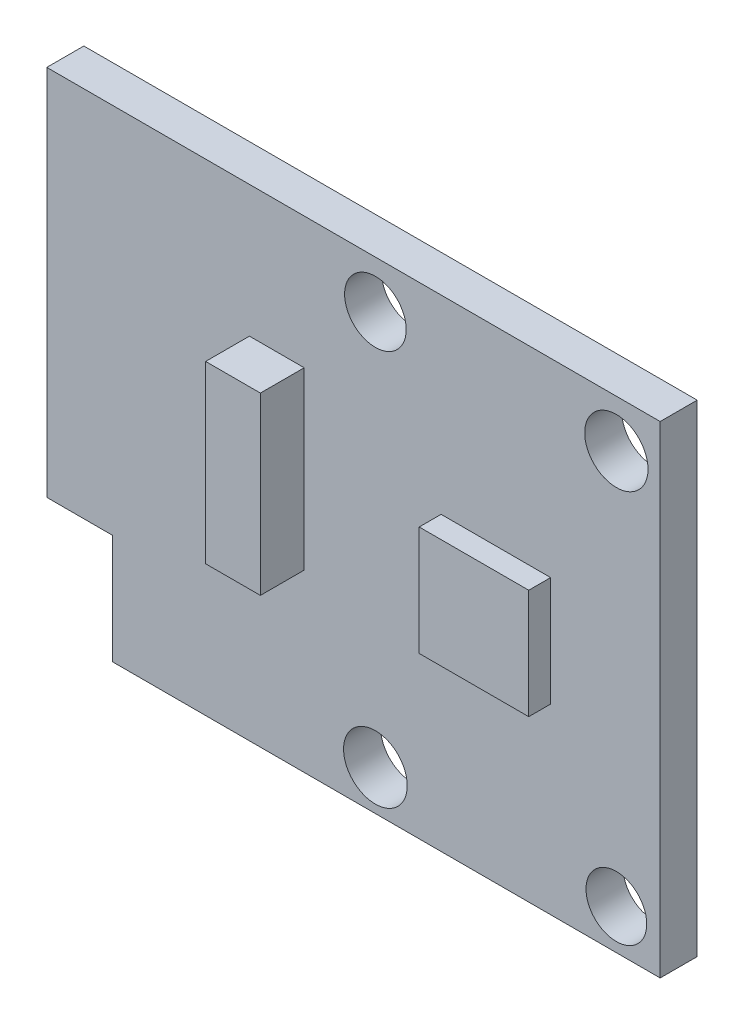
SolidWorks part; units mm, degrees
ref_plane "Front Plane" through (0, 0, 0) normal (0, 0, 1) x (1, 0, 0)
ref_plane "Top Plane" through (0, 0, 0) normal (0, 1, 0) x (1, 0, 0)
ref_plane "Right Plane" through (0, 0, 0) normal (1, 0, 0) x (0, 0, -1)
sketch "Sketch1" plane through (0, 0, 0) normal (0, 0, 1) x (1, 0, 0)
  line L1 (0, 0) -> (28, 0)
  line L2 (0, 0) -> (0, 22)
  line L3 (0, 22) -> (28, 22)
  line L4 (28, 0) -> (28, 22)
  dimension "D1" = 22
  dimension "D2" = 28
extrude "Boss-Extrude1" add sketch "Sketch1" along normal blind 1.69
sketch "Sketch2" plane through (0, 0, 1.69) normal (0, 0, 1) x (1, 0, 0)
  line L0 (28, 0) -> (28, 22) construction
  circle A0 centre (26, 19.8345) radius 1.4454
  circle A1 centre (26, 1.8263) radius 1.3859
  circle A2 centre (15, 1.8263) radius 1.4532
  circle A3 centre (15, 19.8345) radius 1.4063
  dimension "D1" = 2
  dimension "D2" = 11
extrude "Cut-Extrude1" cut sketch "Sketch2" against normal blind 1.69
sketch "Sketch3" plane through (0, 0, 1.69) normal (0, 0, 1) x (1, 0, 0)
  line L0 (15, 19.8345) -> (26, 19.8345) construction
  line L1 (18, 13.3304) -> (23, 13.3304)
  line L2 (18, 13.3304) -> (18, 8.3304)
  line L3 (18, 8.3304) -> (23, 8.3304)
  line L4 (23, 13.3304) -> (23, 8.3304)
  line L5 (15, 19.8345) -> (15, 1.8263) construction
  point P8 (20.5, 19.8345)
  point P13 (18, 10.8304)
  point P14 (15, 10.8304)
  point P15 (20.5, 13.3304)
  dimension "D1" = 5
  dimension "D2" = 5
extrude "Boss-Extrude2" add sketch "Sketch3" along normal blind 1
sketch "Sketch4" plane through (0, 0, 1.69) normal (0, 0, 1) x (1, 0, 0)
  line L0 (28, 0) -> (28, 22) construction
  line L1 (9.25, 16) -> (11.75, 16)
  line L2 (9.25, 16) -> (9.25, 8)
  line L3 (9.25, 8) -> (11.75, 8)
  line L4 (11.75, 16) -> (11.75, 8)
  line L5 (0, 0) -> (28, 0) construction
  dimension "D1" = 16.25
  dimension "D2" = 2.5
  dimension "D3" = 8
  dimension "D4" = 8
extrude "Boss-Extrude3" add sketch "Sketch4" along normal blind 2
ref_plane "Plane1" through (20.5, 0, 0) normal (1, 0, 0) x (0, 0, -1)
ref_plane "flat plane" through (0, 10.8304, 0) normal (0, 1, 0) x (1, 0, 0)
sketch "Sketch5" plane through (0, 0, 1.69) normal (0, 0, 1) x (1, 0, 0)
  line L0 (0, 22) -> (0, 0) construction
  line L1 (0, 5) -> (3, 5)
  line L2 (0, 5) -> (0, 0)
  line L3 (0, 0) -> (3, 0)
  line L4 (3, 5) -> (3, 0)
  line L5 (0, 0) -> (28, 0) construction
  dimension "D1" = 3
  dimension "D2" = 5
extrude "Cut-Extrude2" cut sketch "Sketch5" against normal blind 10
